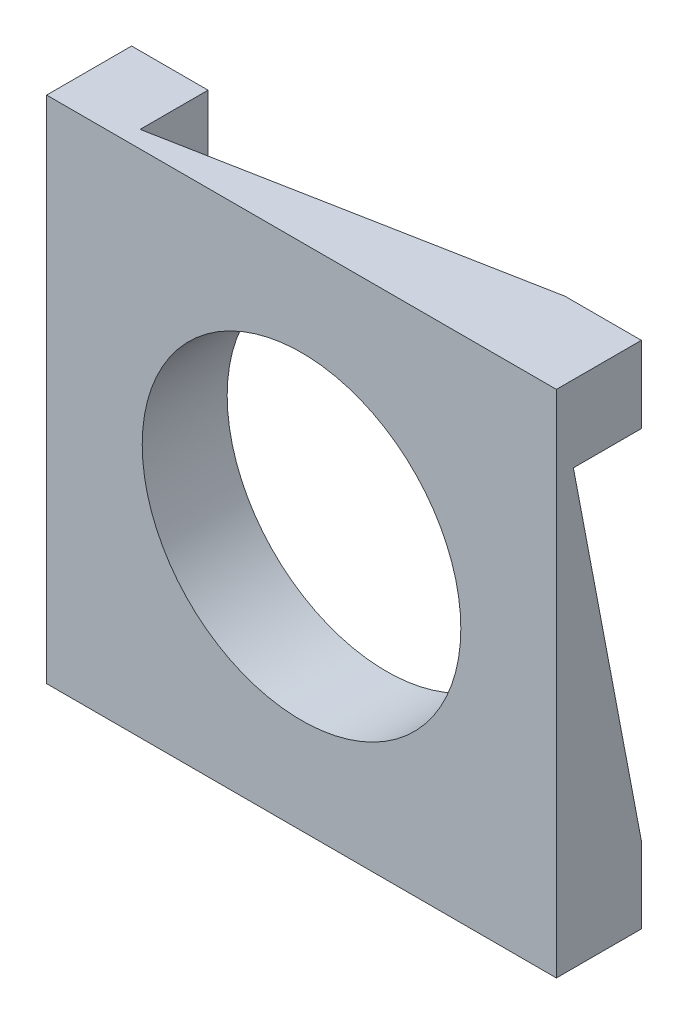
SolidWorks part; units mm, degrees
ref_plane "Alzado" through (0, 0, 0) normal (0, 0, 1) x (1, 0, 0)
ref_plane "Planta" through (0, 0, 0) normal (0, 1, 0) x (1, 0, 0)
ref_plane "Vista lateral" through (0, 0, 0) normal (1, 0, 0) x (0, 0, -1)
sketch "Croquis1" plane through (0, 0, 0) normal (0, 0, 1) x (1, 0, 0)
  line L5 (-275.9526, 317.8595) -> (324.0474, 317.8595)
  line L6 (-275.9526, 317.8595) -> (-275.9526, -282.1405)
  line L7 (-275.9526, -282.1405) -> (324.0474, -282.1405)
  line L8 (324.0474, 317.8595) -> (324.0474, -282.1405)
  line L9 (-275.9526, 317.8595) -> (324.0474, -282.1405) construction
  line L10 (-275.9526, -282.1405) -> (324.0474, 317.8595) construction
  circle A0 centre (24.0474, 17.8595) radius 187.5
  point P0 (0, 0)
  dimension "D1" = 600
  dimension "D2" = 600
extrude "Saliente-Extruir1" add sketch "Croquis1" along normal blind 100
sketch "Croquis2" plane through (-275.9526, 0, 0) normal (-1, 0, 0) x (0, 0, 1)
  line L0 (0, 317.8595) -> (0, -282.1405) construction
  line L1 (0, 227.8595) -> (80, 227.8595)
  line L2 (0, 227.8595) -> (0, -192.1405)
  line L3 (0, -192.1405) -> (80, -192.1405)
  line L4 (80, 227.8595) -> (80, -192.1405)
  line L5 (0, 317.8595) -> (100, 317.8595) construction
  line L6 (0, -282.1405) -> (100, -282.1405) construction
  line L7 (0, 227.8595) -> (80, -192.1405)
  line M7 (0, 317.8595) -> (0, -282.1405)
  dimension "D1" = 80
  dimension "D2" = 90
  dimension "D3" = 90
sketch "Croquis3" plane through (0, -282.1405, 0) normal (0, -1, 0) x (1, 0, 0)
  line L0 (-275.9526, 0) -> (324.0474, 0) construction
  line L1 (-185.9526, 0) -> (234.0474, 0)
  line L2 (-185.9526, 0) -> (-185.9526, 80)
  line L3 (-185.9526, 80) -> (234.0474, 80)
  line L4 (234.0474, 0) -> (234.0474, 80)
  line L5 (-275.9526, 100) -> (-275.9526, 0) construction
  line L6 (324.0474, 100) -> (324.0474, 0) construction
  line L7 (-185.9526, 0) -> (234.0474, 80)
  line M5 (-275.9526, 0) -> (324.0474, 0)
  dimension "D1" = 80
  dimension "D2" = 90
  dimension "D3" = 90
sketch "Croquis4" plane through (324.0474, 0, 0) normal (1, 0, 0) x (0, 0, -1)
  line L0 (0, -282.1405) -> (0, 317.8595) construction
  line L1 (0, -192.1405) -> (-80, -192.1405)
  line L2 (0, -192.1405) -> (0, 227.8595)
  line L3 (0, 227.8595) -> (-80, 227.8595)
  line L4 (-80, -192.1405) -> (-80, 227.8595)
  line L5 (-100, 317.8595) -> (0, 317.8595) construction
  line L6 (-100, -282.1405) -> (0, -282.1405) construction
  line L7 (0, -192.1405) -> (-80, 227.8595)
  line M5 (0, -282.1405) -> (0, 317.8595)
  dimension "D1" = 90
  dimension "D2" = 90
  dimension "D3" = 80
extrude "Cortar-Extruir6" cut sketch "Croquis2" against normal blind 80 contours L7 L3 M7
extrude "Cortar-Extruir7" cut sketch "Croquis3" against normal blind 80 contours L7 L4 M5
extrude "Cortar-Extruir8" cut sketch "Croquis4" against normal blind 80 contours L7 L3 M5
sketch "Croquis6" plane through (0, 317.8595, 0) normal (0, 1, 0) x (1, 0, 0)
  line L0 (324.0474, 0) -> (-275.9526, 0) construction
  line L1 (-185.9526, 0) -> (234.0474, 0)
  line L2 (-185.9526, 0) -> (-185.9526, -80)
  line L3 (-185.9526, -80) -> (234.0474, -80)
  line L4 (234.0474, 0) -> (234.0474, -80)
  line L5 (324.0474, -100) -> (324.0474, 0) construction
  line L6 (-275.9526, -100) -> (-275.9526, 0) construction
  line L7 (234.0474, 0) -> (-185.9526, -80)
  line M5 (324.0474, 0) -> (-275.9526, 0)
  dimension "D1" = 90
  dimension "D2" = 90
  dimension "D3" = 80
extrude "Cortar-Extruir9" cut sketch "Croquis6" against normal blind 80 contours L7 L2 M5
